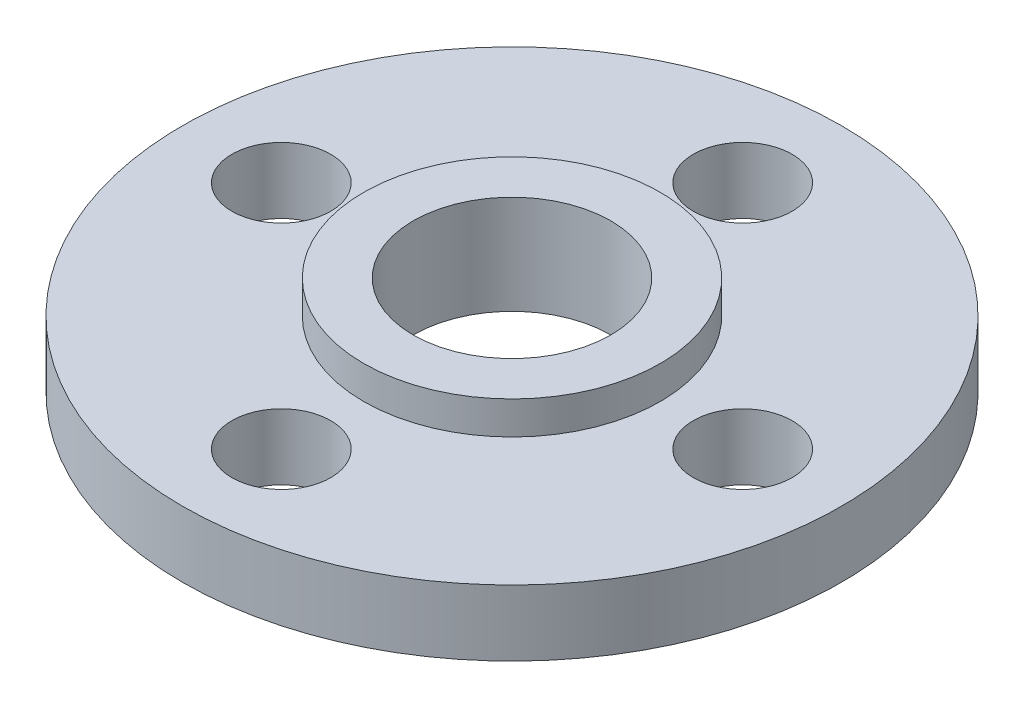
SolidWorks part; units mm, degrees
ref_plane "前视基准面" through (0, 0, 0) normal (0, 0, 1) x (1, 0, 0)
ref_plane "上视基准面" through (0, 0, 0) normal (0, 1, 0) x (1, 0, 0)
ref_plane "右视基准面" through (0, 0, 0) normal (1, 0, 0) x (0, 0, -1)
sketch "草图1" plane through (0, 0, 0) normal (0, 1, 0) x (1, 0, 0)
  circle A0 centre (0, 0) radius 10
extrude "凸台-拉伸1" add sketch "草图1" along normal blind 2
sketch "草图2" plane through (0, 2, 0) normal (0, 1, 0) x (1, 0, 0)
  circle A0 centre (0, 0) radius 3
  circle A1 centre (0, 7) radius 1.5
  circle A2 centre (7, 0) radius 1.5
  circle A3 centre (0, -7) radius 1.5
  circle A4 centre (-7, 0) radius 1.5
  point P14 (0, 0)
  dimension "D1" = 4
  dimension "D2" = 7
  dimension "D3" = 6
extrude "切除-拉伸1" cut sketch "草图2" against normal blind 2
sketch "草图3" plane through (0, 2, 0) normal (0, 1, 0) x (1, 0, 0)
  circle A0 centre (0, 0) radius 3
  circle A1 centre (0, 0) radius 4.5
  dimension "D1" = 6
extrude "凸台-拉伸2" add sketch "草图3" along normal blind 1
